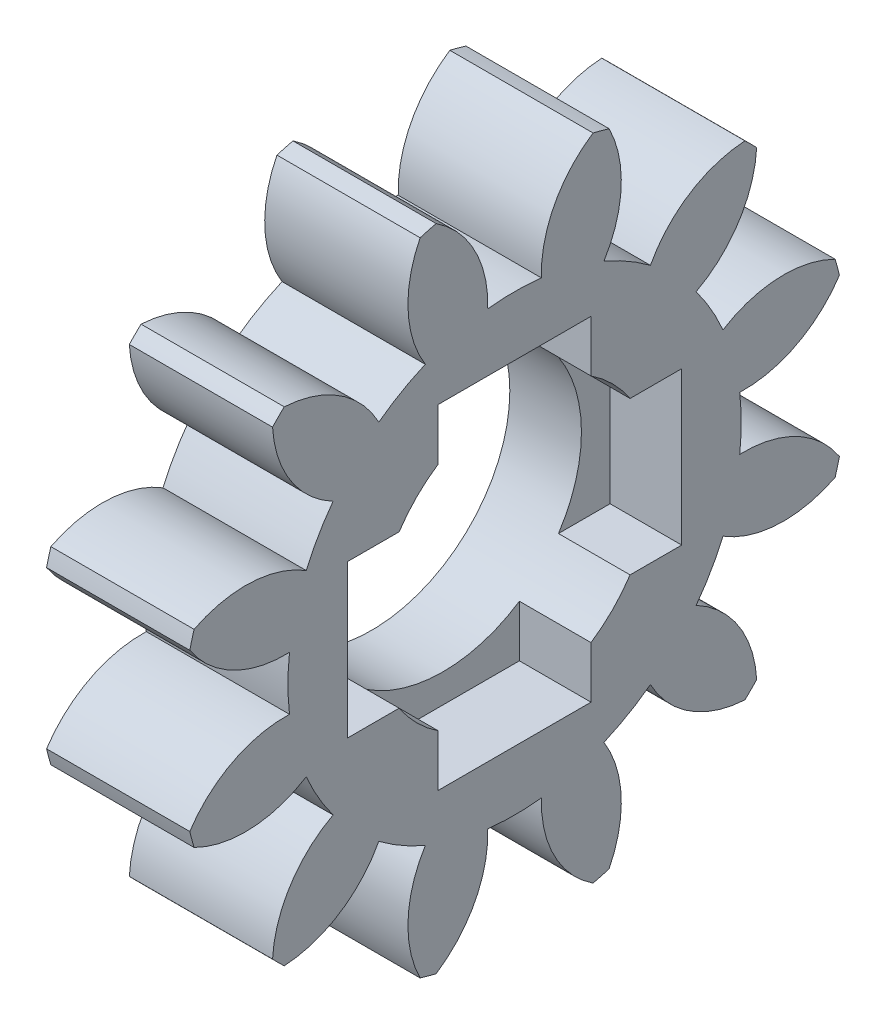
SolidWorks part; units mm, degrees
ref_plane "Plane1" through (0, 0, 0) normal (0, 0, 1) x (1, 0, 0)
ref_plane "Plane2" through (0, 0, 0) normal (0, 1, 0) x (1, 0, 0)
ref_plane "Plane3" through (0, 0, 0) normal (1, 0, 0) x (0, 0, -1)
sketch "HoldingSke" plane through (0, 0, 0) normal (0, 1, 0) x (1, 0, 0)
  line L0 (0, 0) -> (0.9781, -0.2079)
  line L1 (-15, 0) -> (100, 0) construction
  line L2 (0, 0) -> (-2.1039, 2.3779)
  line L3 (0, 0) -> (-11.863, 4.5341)
  line L4 (0, 0) -> (8.4473, 1.7955)
  line L5 (0, 0) -> (-46.8476, -17.4728)
  line L6 (0, 0) -> (-2.4869, -1.6779)
  line L7 (-2.1039, 2.3779) -> (8.6586, 51.2059)
  line L8 (-76.2, 54.61) -> (-75.7, 54.61)
  line L9 (-71.009, 38.7566) -> (-53.1078, 45.2721)
  line L10 (-76.2, 71.12) -> (104.1128, 71.12)
  line L11 (0, 0) -> (-3, 0)
  line L12 (-76.2, 101.6) -> (-76.162, 101.6)
  line L13 (24.9733, 27.94) -> (52.9518, 28.4284)
  line L14 (24.9733, 27.94) -> (24.9743, 27.94)
  line L15 (24.9733, 27.94) -> (100.4006, 29.5858)
  line L16 (-63.627, -1) -> (-12.827, -1)
  circle A0 centre (0, 0) radius 1.5
  circle A1 centre (0, 0) radius 4.749
  circle A2 centre (0, 0) radius 37.5
  circle A3 centre (0, 0) radius 1.5
  dimension "MHD" = 9.498
  dimension "Hub_dia" = 75
  dimension "Bore" = 3
  dimension "MBD" = 3
  dimension "Num_teeth" = 12
  dimension "Pitch" = 1
  dimension "Overall_len" = 50
  dimension "Show_teeth" = 12
  dimension "Thickness" = 3
  dimension "OAL" = 50.0001
  dimension "T_dim" = 0.5
  dimension "Ap" = 20
  dimension "H" = 19.05
  dimension "Pitch_radius" = 180.3128
  dimension "Width" = 3
  dimension "Backlash" = 0.038
  dimension "Addendum_fac" = 1
  dimension "Dedendum_fac" = 1.25
  dimension "Clearance_fac" = 0.25
  dimension "Dedendum_add" = 0.001
  dimension "Module" = 1
sketch "BasProSke" plane through (0, 0, 0) normal (0, 1, 0) x (1, 0, 0)
  line L0 (-10, 0) -> (60, 0) construction
  line L1 (0, 0) -> (0, 7)
  line L2 (0, 0) -> (3, 0)
  line L3 (3, 0) -> (3, 7)
  line L4 (3, 7) -> (0, 7)
  dimension "Thickness" = 3
  dimension "Diameter" = 14
revolve "Base-Revolve" add sketch "BasProSke" angle 360 about L0
sketch "TooCutSke" plane through (0, 0, 0) normal (1, 0, 0) x (0, 0, -1)
  line L1 (0, 0) -> (0, 107) construction
  line L2 (0, 0) -> (-0.8496, 5.9395) construction
  line L3 (0, 0) -> (-3.0836, 11.5081) construction
  line L4 (-0.8496, 5.9395) -> (-1.5418, 5.7541) construction
  arc A0 (0.5622, 4.7156) -> (-0.5622, 4.7156) centre (0, 0) ccw
  arc A1 (1.6729, 6.8233) -> (-1.6729, 6.8233) centre (0, 0) ccw
  circle A2 centre (0, 0) radius 6 construction
  circle A3 centre (0, 0) radius 5.6382 construction
  arc A4 (-0.5622, 4.7156) -> (-1.6729, 6.8233) centre (-2.9608, 4.7982) ccw
  arc A5 (1.6729, 6.8233) -> (0.5622, 4.7156) centre (2.9608, 4.7982) ccw
  dimension "Root_dia" = 9.498
  dimension "Overcut_dia" = 14.0508
  dimension "Pitch_dia" = 12
  dimension "Base_dia" = 11.2763
  dimension "Flank_rad" = 2.4
  dimension "Half_ang" = 15
  dimension "Half_CT" = 0.7167
extrude "ToothCut" cut sketch "TooCutSke" along normal through all
fillet "Breaks" [suppressed] radius 0.02
fillet "RootFillets" [suppressed] radius 0.251
pattern_circular "TeethCuts" count 12 over 360 about axis through (0, 0, 0) along (1, 0, 0) of "ToothCut", "RootFillets", "Breaks"
sketch "HubNeaOneSke" plane through (0, 0, 0) normal (-1, 0, 0) x (0, 0, 1)
  circle A0 centre (0, 0) radius 4.749
  dimension "Diameter" = 9.498
extrude "HubNearOne" [suppressed] add sketch "HubNeaOneSke" along normal blind 47.0001
sketch "HubNeaBotSke" plane through (0, 0, 0) normal (-1, 0, 0) x (0, 0, 1)
  circle A0 centre (0, 0) radius 4.749
  dimension "Diameter" = 9.498
extrude "HubNearBoth" [suppressed] add sketch "HubNeaBotSke" along normal blind 23.5
ref_plane "FarPln" through (3, 0, 0) normal (1, 0, 0) x (0, 0, -1)
sketch "HubFarSke" plane through (3, 0, 0) normal (1, 0, 0) x (0, 0, -1)
  circle A0 centre (0, 0) radius 4.749
  dimension "Diameter" = 9.498
extrude "HubFar" [suppressed] add sketch "HubFarSke" along normal blind 23.5
sketch "BorSke" plane through (0, 0, 0) normal (1, 0, 0) x (0, 0, -1)
  circle A0 centre (0, 0) radius 2.9
  dimension "Diameter" = 5.8
extrude "Bore" cut sketch "BorSke" along normal mid plane 100.0001
sketch "KeySke" plane through (0, 0, 0) normal (1, 0, 0) x (0, 0, -1)
  line L0 (-0.6, 0) -> (-0.6, 2)
  line L1 (-0.6, 2) -> (0.6, 2)
  line L2 (0.6, 2) -> (0.6, 0)
  line L3 (0, 0) -> (0, 34) construction
  line L4 (-0.6, 0) -> (0.6, 0)
  dimension "Offset" = 2
  dimension "Width" = 1.2
extrude "Keyway" [suppressed] cut sketch "KeySke" along normal mid plane 100.0001
pattern_circular "Keyway2" [suppressed] count 2 every 90 about axis through (-10, 0, 0) along (1, 0, 0)
sketch "草图1" plane through (3, 0, 0) normal (1, 0, 0) x (0, 0, -1)
  line L0 (-1.6, -1.6) -> (-1.6, -3.5)
  line L1 (1.6, 3.5) -> (-1.6, 3.5)
  line L2 (1.6, 3.5) -> (1.6, 1.6)
  line L3 (1.6, -3.5) -> (-1.6, -3.5)
  line L4 (-1.6, 3.5) -> (-1.6, 1.6)
  line L5 (1.6, 3.5) -> (-1.6, -3.5) construction
  line L6 (1.6, -3.5) -> (-1.6, 3.5) construction
  line L7 (3.5, 1.6) -> (1.6, 1.6)
  line L8 (3.5, 1.6) -> (3.5, -1.6)
  line L9 (3.5, -1.6) -> (1.6, -1.6)
  line L10 (-3.5, 1.6) -> (-3.5, -1.6)
  line L11 (3.5, 1.6) -> (-3.5, -1.6) construction
  line L12 (3.5, -1.6) -> (-3.5, 1.6) construction
  line L13 (-1.6, -1.6) -> (-3.5, -1.6)
  line L14 (1.6, -1.6) -> (1.6, -3.5)
  line L15 (-1.6, 1.6) -> (-3.5, 1.6)
  point P0 (0, 0)
  point P6 (0, 0)
  dimension "D1" = 3.2
  dimension "D2" = 7
  dimension "D3" = 7
  dimension "D4" = 3.2
extrude "切除-拉伸1" cut sketch "草图1" against normal blind 1.5
equation "' \"Module@HoldingSke\" = 6.35"
equation "' \"Num_teeth@HoldingSke\" = 12"
equation "' \"Ap@HoldingSke\" =  20"
equation "' \"Ap@HoldingSke\" = 20"
equation "' \"Width@HoldingSke\" = 0.5 * 25.4"
equation "' \"Hub_dia@HoldingSke\"= 1 * 25.4"
equation "' \"Hub_dia@HoldingSke\" = 1 * 25.4"
equation "' \"Overall_len@HoldingSke\" = 1.0 * 25.4"
equation "' \"Bore@HoldingSke\" = 0.75 * 25.4"
equation "' \"T_dim@HoldingSke\" = 0.1 * 25.4"
equation "' \"Width@KeySke\" = 0.25 * 25.4"
equation "' \"Show_teeth@HoldingSke\" = 13"
equation "' \"Backlash@HoldingSke\" = 0.009 * 25.4"
equation "' \"Addendum_fac@HoldingSke\" = 1.0"
equation "' \"Dedendum_fac@HoldingSke\" = 1.25"
equation "' \"Dedendum_add@HoldingSke\" = 0.00005 * 25.4"
equation "' \"Clearance_fac@HoldingSke\" = 0.25"
equation "\"Pitch@HoldingSke\" = 1 / \"Module@HoldingSke\""
equation "\"Overcut_dia@TooCutSke\" = (\"Num_teeth@HoldingSke\" + 2 * \"Addendum_fac@HoldingSke\") / \"Pitch@HoldingSke\" + 0.002 * 25.4"
equation "\"Pitch_dia@TooCutSke\" = \"Num_teeth@HoldingSke\" / \"Pitch@HoldingSke\""
equation "\"Base_dia@TooCutSke\" = \"Num_teeth@HoldingSke\" / \"Pitch@HoldingSke\" * cos((\"Ap@HoldingSke\"  * 3.14159265 / 180))"
equation "\"Root_dia@TooCutSke\" = (\"Num_teeth@HoldingSke\" + 2) / \"Pitch@HoldingSke\" - 2 * (\"Addendum_fac@HoldingSke\" + \"Dedendum_fac@HoldingSke\") / \"Pitch@HoldingSke\" - \"Dedendum_add@HoldingSke\" * 2"
equation "\"Half_ang@TooCutSke\" = 180 / \"Num_teeth@HoldingSke\""
equation "\"Half_CT@TooCutSke\" = \"Num_teeth@HoldingSke\" / \"Pitch@HoldingSke\" * sin((3.14159265 / 2 / \"Num_teeth@HoldingSke\")) / 2 - 7 * \"Backlash@HoldingSke\" / 4"
equation "\"Flank_rad@TooCutSke\" = \"Num_teeth@HoldingSke\" / \"Pitch@HoldingSke\" / 5"
equation "\"Radius@RootFillets\" = \"Clearance_fac@HoldingSke\" / \"Pitch@HoldingSke\" + \"Dedendum_add@HoldingSke\""
equation "\"Break_rad@Breaks\" = 0.02 / \"Pitch@HoldingSke\""
equation "\"Thickness@HoldingSke\" = \"Width@HoldingSke\""
equation "\"OAL@HoldingSke\" = \"Thickness@HoldingSke\""
equation "\"MHD@HoldingSke\" = (\"Num_teeth@HoldingSke\" + 2) / \"Pitch@HoldingSke\" - 2 * (\"Addendum_fac@HoldingSke\" + \"Dedendum_fac@HoldingSke\")  / \"Pitch@HoldingSke\" - \"Dedendum_add@HoldingSke\" * 2"
equation "\"MBD@HoldingSke\" = (\"Num_teeth@HoldingSke\" + 2) / \"Pitch@HoldingSke\" - 2 * (\"Addendum_fac@HoldingSke\" + \"Dedendum_fac@HoldingSke\")  / \"Pitch@HoldingSke\" - \"Dedendum_add@HoldingSke\" * 2 - 0.002 * 25.4"
equation "\"MHD@HoldingSke\" = ((sgn( \"MHD@HoldingSke\" - \"Hub_dia@HoldingSke\" )-1)*( \"MHD@HoldingSke\" - \"Hub_dia@HoldingSke\" ))/-2+ \"Hub_dia@HoldingSke\""
equation "\"MBD@HoldingSke\" = ((sgn( \"MBD@HoldingSke\" - \"Bore@HoldingSke\" )-1)*( \"MBD@HoldingSke\" - \"Bore@HoldingSke\" ))/-2+ \"Bore@HoldingSke\""
equation "\"OAL@HoldingSke\" = ((sgn( \"OAL@HoldingSke\" - \"Overall_len@HoldingSke\" )+1)*( \"OAL@HoldingSke\" - \"Overall_len@HoldingSke\" ))/2 + \"Overall_len@HoldingSke\" + 0.000002 * 25.4"
equation "\"Num_teeth@TeethCuts\" = int( \"Show_teeth@HoldingSke\" ) + 1"
equation "\"Num_teeth@TeethCuts\" = ((sgn( \"Num_teeth@TeethCuts\" - \"Num_teeth@HoldingSke\" )-1)*( \"Num_teeth@TeethCuts\" - \"Num_teeth@HoldingSke\" ))/-2+ \"Num_teeth@HoldingSke\""
equation "\"Num_teeth@TeethCuts\" = ((sgn( \"Num_teeth@TeethCuts\" - 2.0)+1)*( \"Num_teeth@TeethCuts\" - 2.0))/2 +2.0"
equation "\"Angle@TeethCuts\" = 360.0 / \"Num_teeth@HoldingSke\""
equation "\"Diameter@BasProSke\" = (\"Num_teeth@HoldingSke\" + 2 * \"Addendum_fac@HoldingSke\") / \"Pitch@HoldingSke\""
equation "\"Thickness@BasProSke\"  = \"Thickness@HoldingSke\""
equation "' \"Fillet_rad@BasProSke\" =  \"Thickness@HoldingSke\" * 0.05"
equation "' \"Fillet_rad@BasProSke\" = \"Thickness@HoldingSke\" * 0.05"
equation "\"MHD@HoldingSke\" = ((sgn( \"MHD@HoldingSke\" - \"Root_dia@TooCutSke\" )-1)*( \"MHD@HoldingSke\" - \"Root_dia@TooCutSke\" ))/-2+ \"Root_dia@TooCutSke\""
equation "\"Diameter@HubNeaOneSke\" = \"MHD@HoldingSke\""
equation "\"Length@HubNearOne\" = \"OAL@HoldingSke\" - \"Thickness@BasProSke\""
equation "\"Diameter@HubNeaBotSke\" = \"MHD@HoldingSke\""
equation "\"Length@HubNearBoth\" = ( \"OAL@HoldingSke\" - \"Thickness@BasProSke\" ) / 2.0"
equation "\"Thickness@FarPln\" = \"Thickness@BasProSke\""
equation "\"Diameter@HubFarSke\" = \"MHD@HoldingSke\""
equation "\"Length@HubFar\" = ( \"OAL@HoldingSke\" - \"Thickness@BasProSke\" ) / 2.0"
equation "\"D1@Bore\" = \"OAL@HoldingSke\" * 2.0"
equation "\"D1@Keyway\" = \"OAL@HoldingSke\" * 2.0"
equation "\"Offset@KeySke\" = \"T_dim@HoldingSke\" + \"MBD@HoldingSke\" / 2.0"
